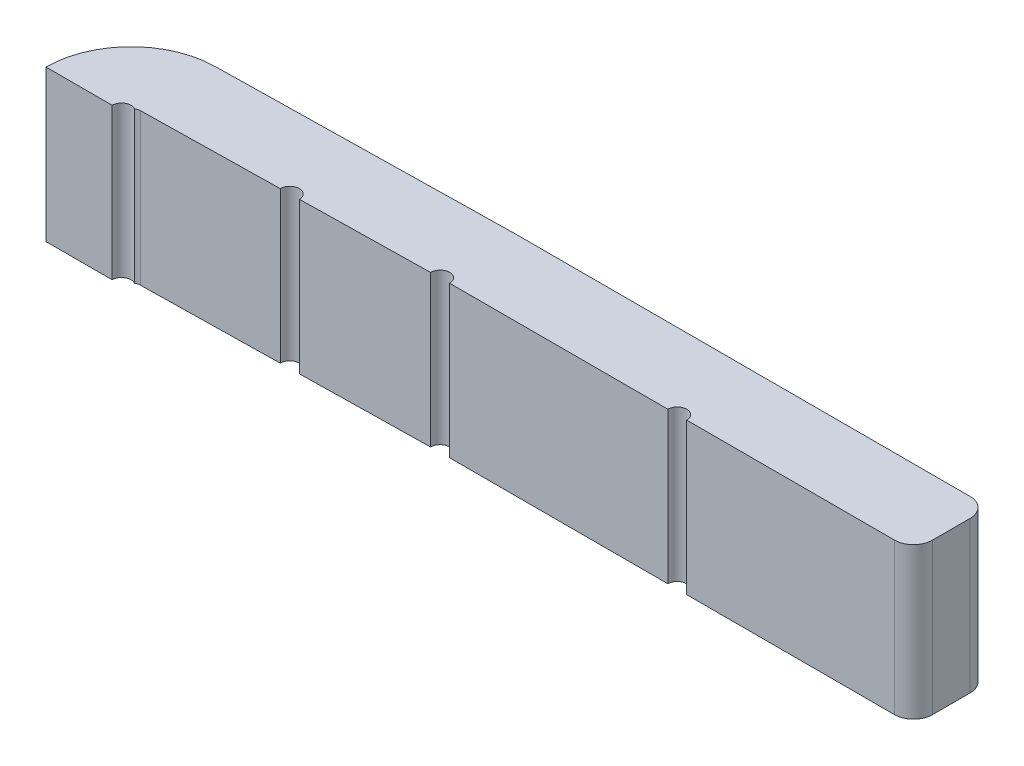
SolidWorks part; units mm, degrees
material "Commercially Pure titanium (Ti-55)  UNS R50550*"
ref_plane "Front Plane" through (0, 0, 0) normal (0, 0, 1) x (1, 0, 0)
ref_plane "Top Plane" through (0, 0, 0) normal (0, 1, 0) x (1, 0, 0)
ref_plane "Right Plane" through (0, 0, 0) normal (1, 0, 0) x (0, 0, -1)
sketch "Sketch1" plane through (0, 0, 0) normal (0, 1, 0) x (1, 0, 0)
  line L0 (-0.2, 0) -> (0.2, 0)
  line L1 (0.2421, 0.4499) -> (1.7975, 0.4771)
  line L2 (1.7975, 0.4771) -> (1.8045, 0.0771) construction
  line L3 (1.8045, 0.0771) -> (0.2491, 0.05)
  line L4 (1.8133, 0.4772) -> (1.8133, 0.0772) construction
  line L7 (1.8133, 0.4772) -> (4.3133, 0.4772)
  line L8 (4.3133, 0.4772) -> (4.3133, 0.0772)
  line L9 (4.3133, 0.0772) -> (1.8133, 0.0772)
  arc A0 (-0.2, 0) -> (0.2421, 0.4499) centre (0.25, 0) cw
  arc A1 (0.2491, 0.05) -> (0.2, 0) centre (0.25, 0) ccw
  arc A2 (1.7975, 0.4771) -> (1.8133, 0.4772) centre (1.8133, -0.4228) cw
  arc A3 (1.8133, 0.0772) -> (1.8045, 0.0771) centre (1.8133, -0.4228) ccw
  point P0 (4.3, 2)
  point P3 (0, 0)
  point P4 (0, 0)
  dimension "D6" = 1
  dimension "D7" = 2.5
  dimension "D3" = 0.4
  dimension "D4" = 0.05
  dimension "D5" = 0.5
  dimension "D1" = 90
  dimension "D2" = 90
  dimension "D8" = 1.5556
extrude "Boss-Extrude1" add sketch "Sketch1" along normal blind 0.8
mirror "Mirror1" of "Boss-Extrude1"
sketch "Sketch2" plane through (0, 0.8, 0) normal (0, 1, 0) x (1, 0, 0)
  line L0 (1.8133, 0.0772) -> (4.3133, 0.0772) construction
  line L1 (0.2491, 0.05) -> (1.8045, 0.0771) construction
  circle A0 centre (0.2, 0) radius 0.05
  arc A1 (0.2491, 0.05) -> (0.2491, -0.05) centre (0.25, 0) ccw construction
  circle A2 centre (1.8089, 0.0772) radius 0.05
  arc A3 (1.8133, 0.0772) -> (1.8045, 0.0771) centre (1.8133, -0.4228) ccw construction
  circle A4 centre (3.0633, 0.0772) radius 0.05
  circle A5 centre (1.0268, 0.0636) radius 0.05
  dimension "D1" = 0.1
extrude "Cut-Extrude1" cut sketch "Sketch2" against normal blind 10
mirror "Mirror2" about plane through (0, 0, 0) normal (0, 0, 1) of "Cut-Extrude1"
fillet "Fillet2" radius 0.1 4 edges at (4.3133, 0.4, -0.0772) (4.3133, 0.4, -0.4772) (4.3133, 0.4, 0.0772) (4.3133, 0.4, 0.4772)
fillet "Fillet1" [suppressed] radius 0.1
other "SurfaceCut1"
